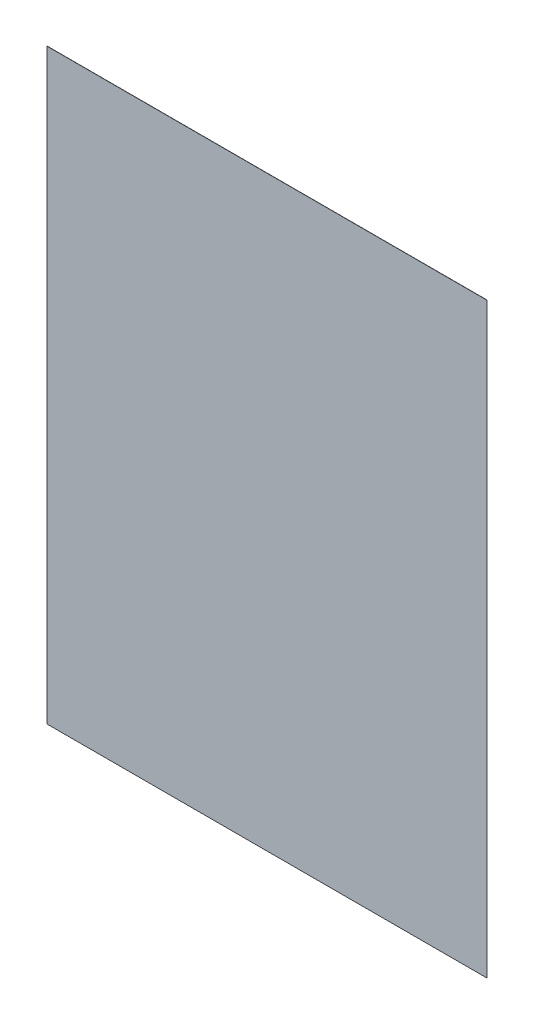
SolidWorks part; units mm, degrees
material "Kapton Film"
ref_plane "Front Plane" through (0, 0, 0) normal (0, 0, 1) x (1, 0, 0)
ref_plane "Top Plane" through (0, 0, 0) normal (0, 1, 0) x (1, 0, 0)
ref_plane "Right Plane" through (0, 0, 0) normal (1, 0, 0) x (0, 0, -1)
sketch "Sketch1" plane through (0, 0, 0) normal (0, 0, 1) x (1, 0, 0)
  line L1 (-77, 102.75) -> (77, 102.75)
  line L2 (-77, 102.75) -> (-77, -102.75)
  line L3 (-77, -102.75) -> (77, -102.75)
  line L4 (77, 102.75) -> (77, -102.75)
  line L5 (-77, 102.75) -> (77, -102.75) construction
  line L6 (-77, -102.75) -> (77, 102.75) construction
  point P0 (0, 0)
  dimension "D1" = 154
  dimension "D2" = 205.5
extrude "Body" add sketch "Sketch1" along normal blind 0.0686
